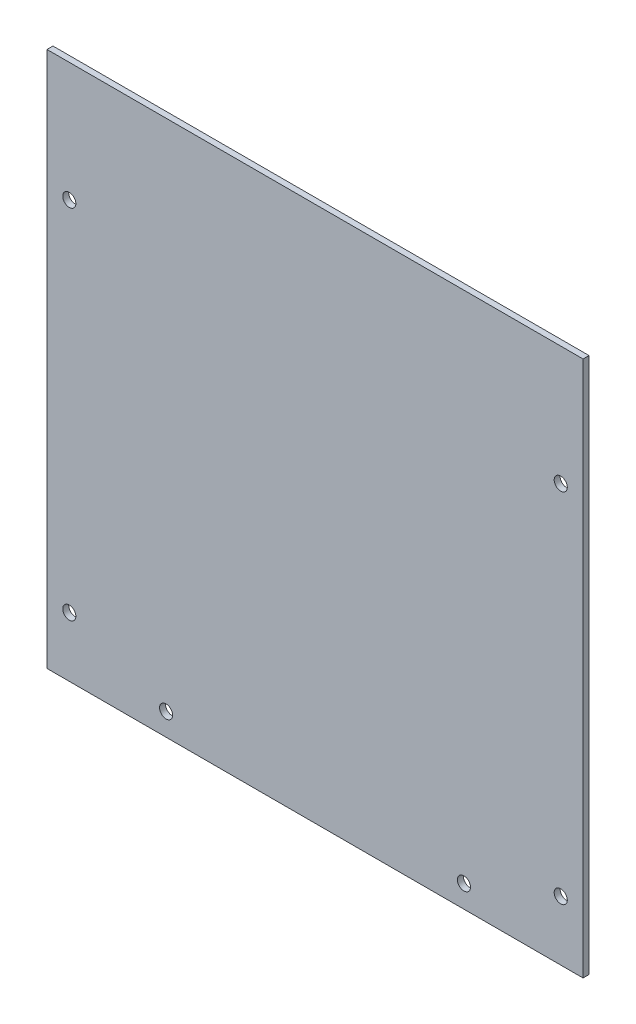
SolidWorks part; units mm, degrees
ref_plane "正面" through (0, 0, 0) normal (0, 0, 1) x (1, 0, 0)
ref_plane "平面" through (0, 0, 0) normal (0, 1, 0) x (1, 0, 0)
ref_plane "右側面" through (0, 0, 0) normal (1, 0, 0) x (0, 0, -1)
sketch "ｽｹｯﾁ1" plane through (0, 0, 0) normal (0, 0, 1) x (1, 0, 0)
  line L1 (-90, 90) -> (90, 90)
  line L2 (-90, 90) -> (-90, -90)
  line L3 (-90, -90) -> (90, -90)
  line L4 (90, 90) -> (90, -90)
  line L5 (-90, 90) -> (90, -90) construction
  line L6 (-90, -90) -> (90, 90) construction
  point P0 (0, 0)
  dimension "D1" = 180
  dimension "D2" = 180
extrude "ﾎﾞｽ - 押し出し1" add sketch "ｽｹｯﾁ1" along normal blind 2
sketch "ｽｹｯﾁ2" plane through (0, 0, 2) normal (0, 0, 1) x (1, 0, 0)
  line L1 (-90, -90) -> (-50, -90)
  line L2 (-90, -90) -> (-90, -82.5)
  line L3 (-90, -82.5) -> (-50, -82.5)
  line L4 (-50, -90) -> (-50, -82.5)
  line L5 (90, -90) -> (50, -90)
  line L6 (90, -90) -> (90, -82.5)
  line L7 (90, -82.5) -> (50, -82.5)
  line L8 (50, -90) -> (50, -82.5)
  circle A0 centre (-50, -82.5) radius 2.2
  circle A1 centre (50, -82.5) radius 2.2
  dimension "D5" = 4.4
  dimension "D6" = 4.4
  dimension "D1" = 7.5
  dimension "D2" = 7.5
  dimension "D3" = 40
  dimension "D4" = 40
extrude "ｶｯﾄ - 押し出し1" cut sketch "ｽｹｯﾁ2" against normal blind 140 contours L4 A0 L3 | L3 A0 L4 | L7 A1 L8 | L8 A1 L7
sketch "ｽｹｯﾁ3" plane through (0, 0, 2) normal (0, 0, 1) x (1, 0, 0)
  line L0 (-90, -90) -> (-82.5, -90)
  line L1 (-90, -90) -> (90, -90) construction
  line L2 (-82.5, -90) -> (-82.5, -70)
  line L3 (-82.5, -70) -> (-82.5, 50)
  line L4 (90, -90) -> (82.5, -90)
  line L5 (82.5, -90) -> (82.5, -70)
  line L6 (82.5, -70) -> (82.5, 50)
  circle A0 centre (-82.5, 50) radius 2.2
  circle A1 centre (82.5, 50) radius 2.2
  circle A2 centre (82.5, -70) radius 2.2
  circle A3 centre (-82.5, -70) radius 2.2
  dimension "D7" = 4.4
  dimension "D8" = 4.4
  dimension "D9" = 4.4
  dimension "D10" = 4.4
  dimension "D1" = 7.5
  dimension "D2" = 20
  dimension "D3" = 120
  dimension "D4" = 7.5
  dimension "D5" = 20
  dimension "D6" = 120
extrude "ｶｯﾄ - 押し出し2" cut sketch "ｽｹｯﾁ3" against normal blind 160
